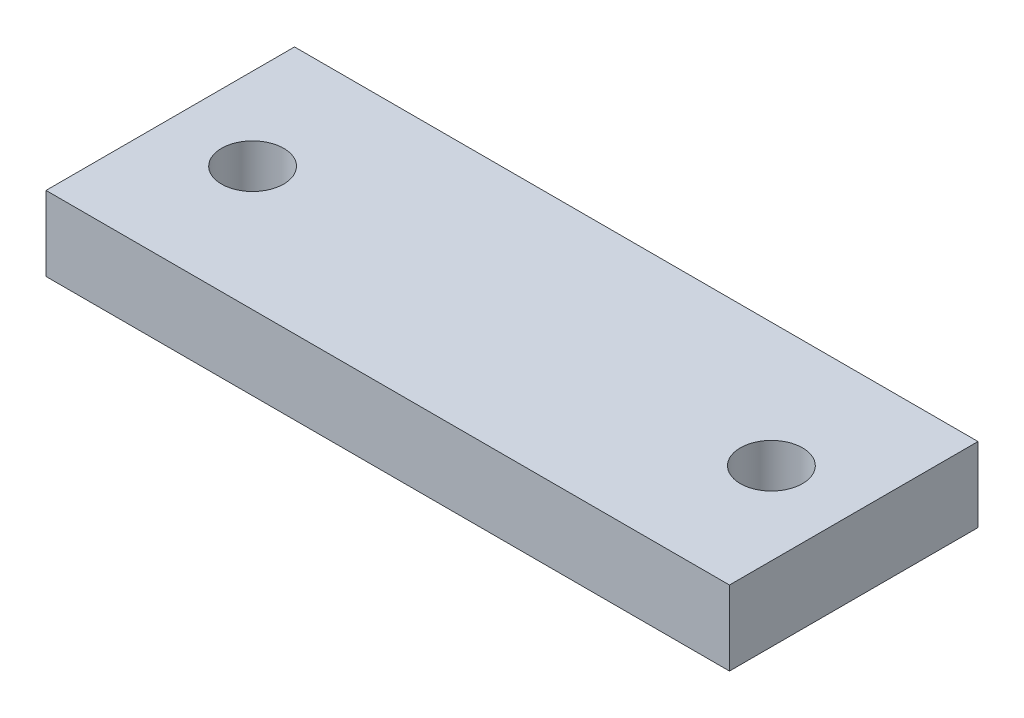
SolidWorks part; units mm, degrees
ref_plane "Front Plane" through (0, 0, 0) normal (0, 0, 1) x (1, 0, 0)
ref_plane "Top Plane" through (0, 0, 0) normal (0, 1, 0) x (1, 0, 0)
ref_plane "Right Plane" through (0, 0, 0) normal (1, 0, 0) x (0, 0, -1)
sketch "Sketch1" plane through (0, 0, 0) normal (0, 1, 0) x (1, 0, 0)
  line L1 (-27.5, -10) -> (27.5, -10)
  line L2 (-27.5, -10) -> (-27.5, 10)
  line L3 (-27.5, 10) -> (27.5, 10)
  line L4 (27.5, -10) -> (27.5, 10)
  line L5 (-27.5, -10) -> (27.5, 10) construction
  line L6 (-27.5, 10) -> (27.5, -10) construction
  point P0 (0, 0)
  dimension "D1" = 55
  dimension "D2" = 20
extrude "Boss-Extrude1" add sketch "Sketch1" along normal blind 6
sketch "Sketch2" plane through (0, 6, 0) normal (0, 1, 0) x (1, 0, 0)
  line L0 (-27.5, 10) -> (-27.5, -10) construction
  line L1 (27.5, -10) -> (27.5, 10) construction
  circle A0 centre (-20.875, 0) radius 2.5
  circle A1 centre (20.875, 0) radius 2.5
  dimension "D3" = 5
  dimension "D4" = 5
  dimension "D1" = 6.625
  dimension "D2" = 6.625
extrude "Cut-Extrude1" cut sketch "Sketch2" against normal blind 6
